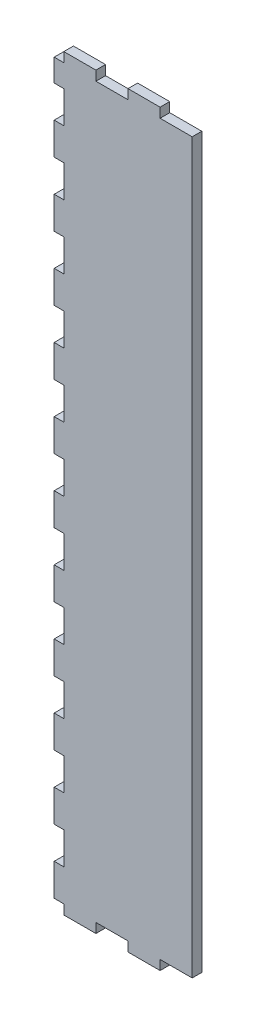
SolidWorks part; units mm, degrees
ref_plane "Front Plane" through (0, 0, 0) normal (0, 0, 1) x (1, 0, 0)
ref_plane "Top Plane" through (0, 0, 0) normal (0, 1, 0) x (1, 0, 0)
ref_plane "Right Plane" through (0, 0, 0) normal (1, 0, 0) x (0, 0, -1)
sketch "Sketch1" plane through (0, 0, 0) normal (0, 0, 1) x (1, 0, 0)
  line L1 (0, 0) -> (40, 0)
  line L2 (0, 0) -> (0, 227)
  line L3 (0, 227) -> (40, 227)
  line L4 (40, 0) -> (40, 227)
  dimension "D1" = 40
  dimension "D2" = 227
extrude "Boss-Extrude1" add sketch "Sketch1" along normal blind 3
sketch "Sketch2" plane through (0, 0, 0) normal (0, -1, 0) x (1, 0, 0)
  line L0 (0, 0) -> (40, 0) construction
  line L1 (30, 0) -> (20, 0)
  line L2 (30, 0) -> (30, 3)
  line L3 (30, 3) -> (20, 3)
  line L4 (20, 0) -> (20, 3)
  line L5 (0, 3) -> (40, 3) construction
  line L6 (40, 3) -> (40, 0) construction
  dimension "D1" = 10
  dimension "D2" = 10
extrude "Boss-Extrude2" add sketch "Sketch2" along normal blind 3
pattern_linear "LPattern1" count 2 spacing 20 along (-1, 0, 0) of "Boss-Extrude2"
sketch "Sketch3" plane through (0, 227, 0) normal (0, 1, 0) x (1, 0, 0)
  line L0 (40, -3) -> (0, -3) construction
  line L1 (30, -3) -> (20, -3)
  line L2 (30, -3) -> (30, 0)
  line L3 (30, 0) -> (20, 0)
  line L4 (20, -3) -> (20, 0)
  line L5 (40, 0) -> (0, 0) construction
  line L6 (40, -3) -> (40, 0) construction
  point P10 (40, -1.5)
  dimension "D1" = 10
  dimension "D2" = 10
extrude "Boss-Extrude3" add sketch "Sketch3" along normal blind 3
pattern_linear "LPattern2" count 2 spacing 20 along (-1, 0, 0) of "Boss-Extrude3"
sketch "Sketch4" plane through (0, 0, 0) normal (-1, 0, 0) x (0, 0, 1)
  line L0 (3, 230) -> (3, -3) construction
  line L1 (0, 0) -> (3, 0)
  line L2 (0, 0) -> (0, 10)
  line L3 (0, 10) -> (3, 10)
  line L4 (3, 0) -> (3, 10)
  dimension "D1" = 10
extrude "Boss-Extrude4" add sketch "Sketch4" along normal blind 3
pattern_linear "LPattern3" count 12 spacing 20 along (0, 1, 0) of "Boss-Extrude4"
sketch "Esquisse1" plane through (0, 0, 3) normal (0, 0, 1) x (1, 0, 0)
  line L1 (-3, 230) -> (0, 230)
  line L2 (-3, 230) -> (-3, 227)
  line L3 (-3, 227) -> (0, 227)
  line L4 (0, 230) -> (0, 227)
  dimension "D1" = 3
  dimension "D2" = 3
extrude "Enlèv. mat.-Extru.1" cut sketch "Esquisse1" against normal through all
